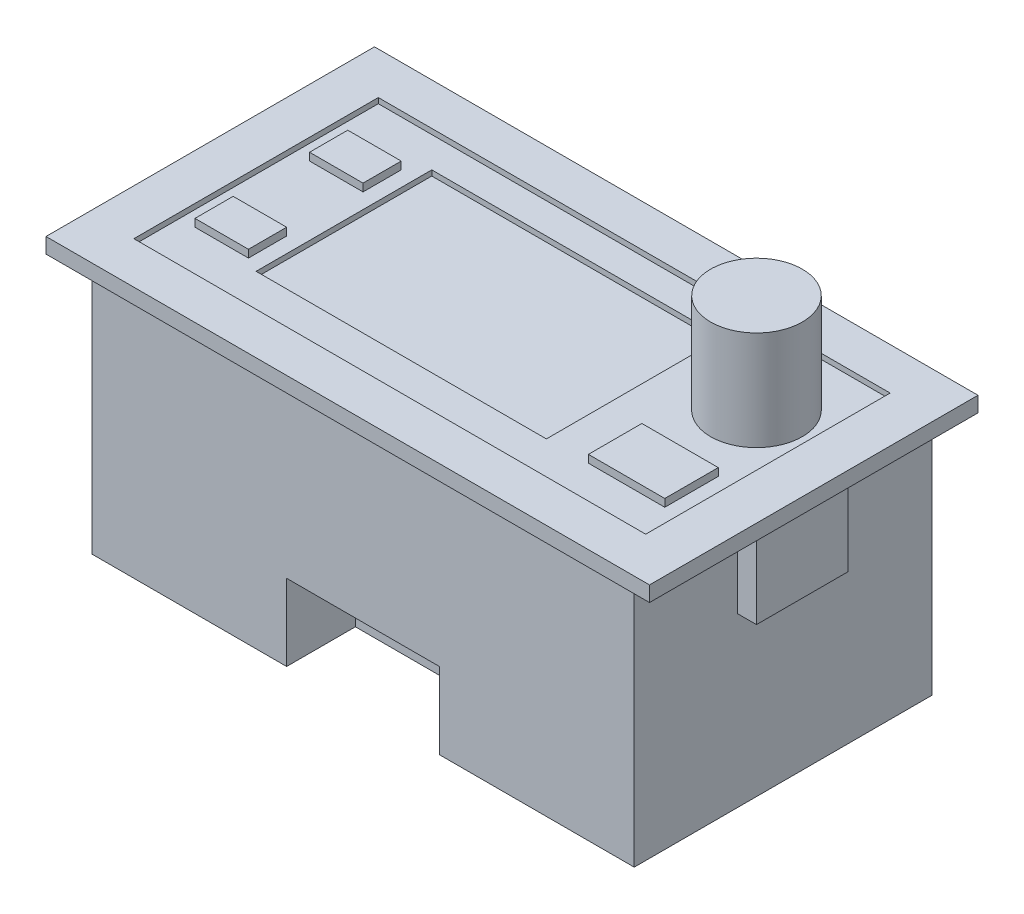
SolidWorks part; units mm, degrees
ref_plane "Front Plane" through (0, 0, 0) normal (0, 0, 1) x (1, 0, 0)
ref_plane "Top Plane" through (0, 0, 0) normal (0, 1, 0) x (1, 0, 0)
ref_plane "Right Plane" through (0, 0, 0) normal (1, 0, 0) x (0, 0, -1)
sketch "Sketch2" plane through (0, 0, 0) normal (0, 1, 0) x (1, 0, 0)
  line L1 (0, 0) -> (79, 0)
  line L2 (0, 0) -> (0, 43)
  line L3 (0, 43) -> (79, 43)
  line L4 (79, 0) -> (79, 43)
  dimension "D1" = 43
  dimension "D2" = 79
extrude "Boss-Extrude1" add sketch "Sketch2" along normal blind 2
sketch "Sketch3" plane through (0, 2, 0) normal (0, 1, 0) x (1, 0, 0)
  line L0 (39.5, 43) -> (39.5, 0) construction
  line L1 (79, 43) -> (0, 43) construction
  line L2 (0, 0) -> (79, 0) construction
  line L3 (0, 21.5) -> (79, 21.5) construction
  line L4 (0, 43) -> (0, 0) construction
  line L5 (79, 0) -> (79, 43) construction
  line L7 (6, 37.5) -> (73, 37.5)
  line L8 (6, 37.5) -> (6, 5.5)
  line L9 (6, 5.5) -> (73, 5.5)
  line L10 (73, 37.5) -> (73, 5.5)
  line L11 (6, 37.5) -> (73, 5.5) construction
  line L12 (6, 5.5) -> (73, 37.5) construction
  point P12 (39.5, 21.5)
  dimension "D1" = 32
  dimension "D2" = 67
extrude "Cut-Extrude1" cut sketch "Sketch3" against normal blind 0.7
sketch "Sketch4" plane through (0, 1.3, 0) normal (0, 1, 0) x (1, 0, 0)
  line L0 (6, 21.5) -> (17, 21.5) construction
  line L1 (6, 37.5) -> (6, 5.5) construction
  line L2 (17, 5.5) -> (17, 10.5) construction
  line L3 (6, 5.5) -> (73, 5.5) construction
  line L5 (17, 10.5) -> (55, 10.5)
  line L6 (17, 10.5) -> (17, 33.5)
  line L7 (17, 33.5) -> (55, 33.5)
  line L8 (55, 10.5) -> (55, 33.5)
  dimension "D1" = 11
  dimension "D2" = 5
  dimension "D3" = 23
  dimension "D4" = 38
extrude "Cut-Extrude2" cut sketch "Sketch4" against normal blind 0.7
sketch "Sketch7" plane through (0, 1.3, 0) normal (0, 1, 0) x (1, 0, 0)
  circle A0 centre (65.5, 27.5) radius 6
  dimension "D3" = 12
extrude "Boss-Extrude2" add sketch "Sketch7" along normal blind 13
sketch "Sketch8" plane through (0, 1.3, 0) normal (0, 1, 0) x (1, 0, 0)
  line L9 (70.5, 17.5) -> (60.5, 17.5)
  line L10 (70.5, 17.5) -> (70.5, 10.5)
  line L11 (70.5, 10.5) -> (60.5, 10.5)
  line L12 (60.5, 17.5) -> (60.5, 10.5)
  line L13 (70.5, 17.5) -> (60.5, 10.5) construction
  line L14 (70.5, 10.5) -> (60.5, 17.5) construction
  dimension "D3" = 7
  dimension "D4" = 10
extrude "Boss-Extrude3" add sketch "Sketch8" along normal blind 1
sketch "Sketch9" plane through (0, 1.3, 0) normal (0, 1, 0) x (1, 0, 0)
  line L0 (8, 37.5) -> (8, 31.5) construction
  line L2 (73, 37.5) -> (6, 37.5) construction
  line L5 (8, 11.5) -> (15, 11.5)
  line L6 (8, 11.5) -> (8, 16.5)
  line L7 (8, 16.5) -> (15, 16.5)
  line L8 (15, 11.5) -> (15, 16.5)
  line L9 (8, 31.5) -> (15, 31.5)
  line L10 (8, 31.5) -> (8, 26.5)
  line L11 (8, 26.5) -> (15, 26.5)
  line L12 (15, 31.5) -> (15, 26.5)
  point P8 (8, 11.5)
  dimension "D1" = 6
  dimension "D2" = 5
  dimension "D3" = 5
  dimension "D4" = 7
  dimension "D5" = 7
extrude "Boss-Extrude4" add sketch "Sketch9" along normal blind 1
sketch "Sketch10" plane through (0, 0, 0) normal (0, -1, 0) x (1, 0, 0)
  line L7 (4, -2) -> (75, -2)
  line L8 (4, -2) -> (4, -41)
  line L9 (4, -41) -> (75, -41)
  line L10 (75, -2) -> (75, -41)
  line L11 (4, -2) -> (75, -41) construction
  line L12 (4, -41) -> (75, -2) construction
  dimension "D1" = 39
  dimension "D2" = 71
extrude "Boss-Extrude5" add sketch "Sketch10" along normal blind 33
sketch "Sketch11" plane through (0, -33, 0) normal (0, -1, 0) x (-1, 0, 0)
  line L0 (-39.5, 2) -> (-39.5, 41) construction
  line L1 (-75, 2) -> (-4, 2) construction
  line L2 (-4, 41) -> (-75, 41) construction
  line L4 (-49.5, -7) -> (-29.5, -7)
  line L5 (-49.5, -7) -> (-49.5, 11)
  line L6 (-49.5, 11) -> (-29.5, 11)
  line L7 (-29.5, -7) -> (-29.5, 11)
  line L8 (-49.5, -7) -> (-29.5, 11) construction
  line L9 (-49.5, 11) -> (-29.5, -7) construction
  dimension "D1" = 20
  dimension "D2" = 18
extrude "Cut-Extrude3" cut sketch "Sketch11" against normal blind 10
sketch "Sketch12" plane through (4, 0, 0) normal (-1, 0, 0) x (0, 0, 1)
  line L0 (-21.5, 0) -> (-21.5, -11) construction
  line L1 (-43, 0) -> (0, 0) construction
  line L3 (-21.5, 0) -> (-27.5, 0)
  line L5 (-21.5, -11) -> (-27.5, -11)
  line L6 (-27.5, 0) -> (-27.5, -11)
  line L7 (-21.5, 0) -> (-15.5, 0)
  line L9 (-21.5, -11) -> (-15.5, -11)
  line L10 (-15.5, 0) -> (-15.5, -11)
  dimension "D1" = 11
  dimension "D2" = 6
  dimension "D3" = 6
extrude "Boss-Extrude6" add sketch "Sketch12" along normal blind 2.5
sketch "Sketch13" plane through (75, 0, 0) normal (1, 0, 0) x (0, 0, -1)
  line L1 (0, 0) -> (43, 0) construction
  line L3 (21.5, 0) -> (15.5, 0)
  line L5 (21.5, -11) -> (15.5, -11)
  line L6 (15.5, 0) -> (15.5, -11)
  line L7 (21.5, 0) -> (27.5, 0)
  line L9 (21.5, -11) -> (27.5, -11)
  line L10 (27.5, 0) -> (27.5, -11)
  dimension "D1" = 11
  dimension "D2" = 6
  dimension "D3" = 6
extrude "Boss-Extrude7" add sketch "Sketch13" along normal blind 2.5
